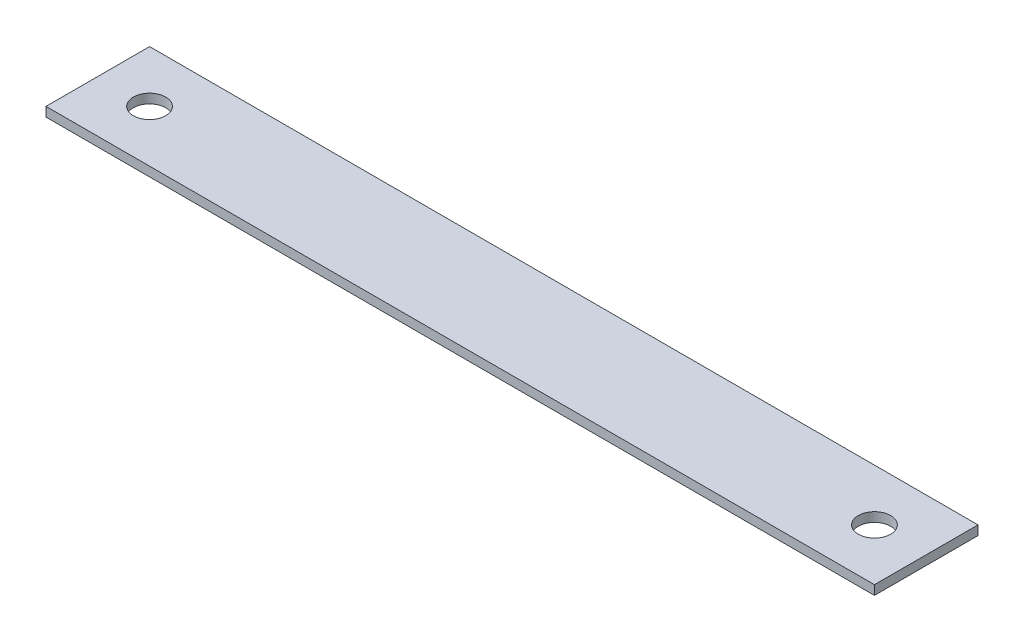
SolidWorks part; units mm, degrees
ref_plane "Front Plane" through (0, 0, 0) normal (0, 0, 1) x (1, 0, 0)
ref_plane "Top Plane" through (0, 0, 0) normal (0, 1, 0) x (1, 0, 0)
ref_plane "Right Plane" through (0, 0, 0) normal (1, 0, 0) x (0, 0, -1)
sketch "Sketch1" plane through (0, 0, 0) normal (0, 1, 0) x (1, 0, 0)
  line L1 (0, 0) -> (203.2, 0)
  line L2 (0, 0) -> (0, 25.4)
  line L3 (0, 25.4) -> (203.2, 25.4)
  line L4 (203.2, 0) -> (203.2, 25.4)
  dimension "D1" = 203.2
  dimension "D2" = 25.4
extrude "Boss-Extrude1" add sketch "Sketch1" along normal blind 2.286
sketch "Sketch2" plane through (0, 2.286, 0) normal (0, 1, 0) x (1, 0, 0)
  line L0 (0, 25.4) -> (0, 0) construction
  line L1 (203.2, 0) -> (203.2, 25.4) construction
  circle A0 centre (12.7, 12.7) radius 3.9688
  circle A1 centre (190.5, 12.7) radius 3.9687
  point P8 (0, 12.7)
  dimension "D1" = 7.9375
  dimension "D2" = 12.7
  dimension "D3" = 12.7
  dimension "D4" = 7.9375
extrude "Cut-Extrude1" cut sketch "Sketch2" against normal through all
